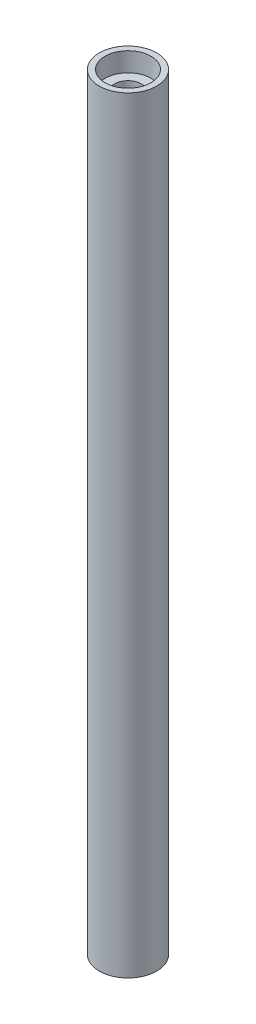
SolidWorks part; units mm, degrees
material "Сплав 2024"
ref_plane "Спереди" through (0, 0, 0) normal (0, 0, 1) x (1, 0, 0)
ref_plane "Сверху" through (0, 0, 0) normal (0, 1, 0) x (1, 0, 0)
ref_plane "Справа" through (0, 0, 0) normal (1, 0, 0) x (0, 0, -1)
sketch "Эскиз1" plane through (0, 0, 0) normal (0, 1, 0) x (1, 0, 0)
  circle A0 centre (0, 0) radius 7.5
  dimension "D1" = 15
extrude "Бобышка-Вытянуть1" add sketch "Эскиз1" along normal blind 200
sketch "Эскиз2" plane through (0, 200, 0) normal (0, 1, 0) x (1, 0, 0)
  circle A0 centre (0, 0) radius 3.5
  dimension "D1" = 7
extrude "Вырез-Вытянуть1" cut sketch "Эскиз2" against normal through all
sketch "Эскиз4" plane through (0, 200, 0) normal (0, 1, 0) x (1, 0, 0)
  circle A0 centre (0, 0) radius 6
  dimension "D1" = 12
extrude "Вырез-Вытянуть3" cut sketch "Эскиз4" against normal blind 5
sketch "Эскиз7" plane through (0, 0, 0) normal (0, -1, 0) x (1, 0, 0)
  circle A0 centre (0, 0) radius 6
  dimension "D1" = 12
extrude "Вырез-Вытянуть4" cut sketch "Эскиз7" against normal blind 5
